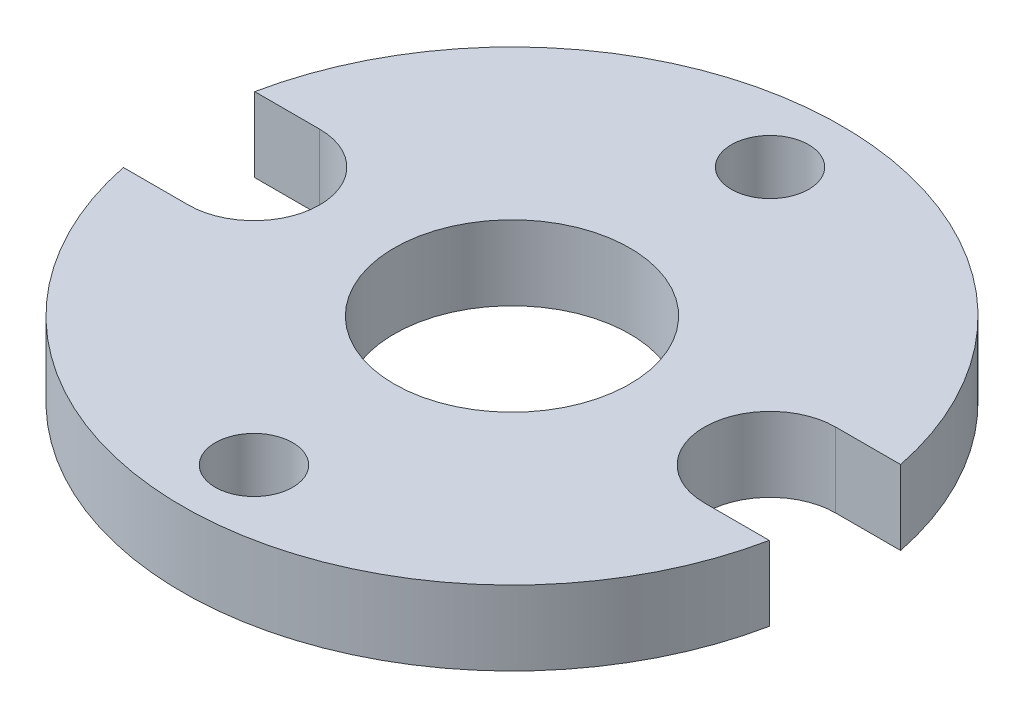
SolidWorks part; units mm, degrees
ref_plane "Front Plane" through (0, 0, 0) normal (0, 0, 1) x (1, 0, 0)
ref_plane "Top Plane" through (0, 0, 0) normal (0, 1, 0) x (1, 0, 0)
ref_plane "Right Plane" through (0, 0, 0) normal (1, 0, 0) x (0, 0, -1)
sketch "Sketch1" plane through (0, 0, 0) normal (0, 1, 0) x (1, 0, 0)
  line L0 (11, 0) -> (-11, 0) construction
  line L1 (-11, 2.8) -> (-13.7682, 2.8)
  line L2 (-11, -2.8) -> (-13.7682, -2.8)
  line L3 (13.7682, 2.8) -> (11, 2.8)
  line L4 (11, -2.8) -> (13.7682, -2.8)
  arc A0 (13.7682, 2.8) -> (-13.7682, 2.8) centre (0, 0) ccw
  circle A1 centre (0, 0) radius 5.025
  arc A2 (11, 2.8) -> (11, -2.8) centre (11, 0) ccw
  arc A3 (-11, -2.8) -> (-11, 2.8) centre (-11, 0) ccw
  arc A4 (-13.7682, -2.8) -> (13.7682, -2.8) centre (0, 0) ccw
  circle A5 centre (0, 11) radius 1.65
  circle A6 centre (0, -11) radius 1.65
  circle A7 centre (0, 0) radius 11 construction
  point P11 (0, 0)
  dimension "D1" = 28.1
  dimension "D2" = 10.05
  dimension "D4" = 5.6
  dimension "D5" = 3.3
  dimension "D3" = 22
extrude "Boss-Extrude1" add sketch "Sketch1" along normal blind 3.175
